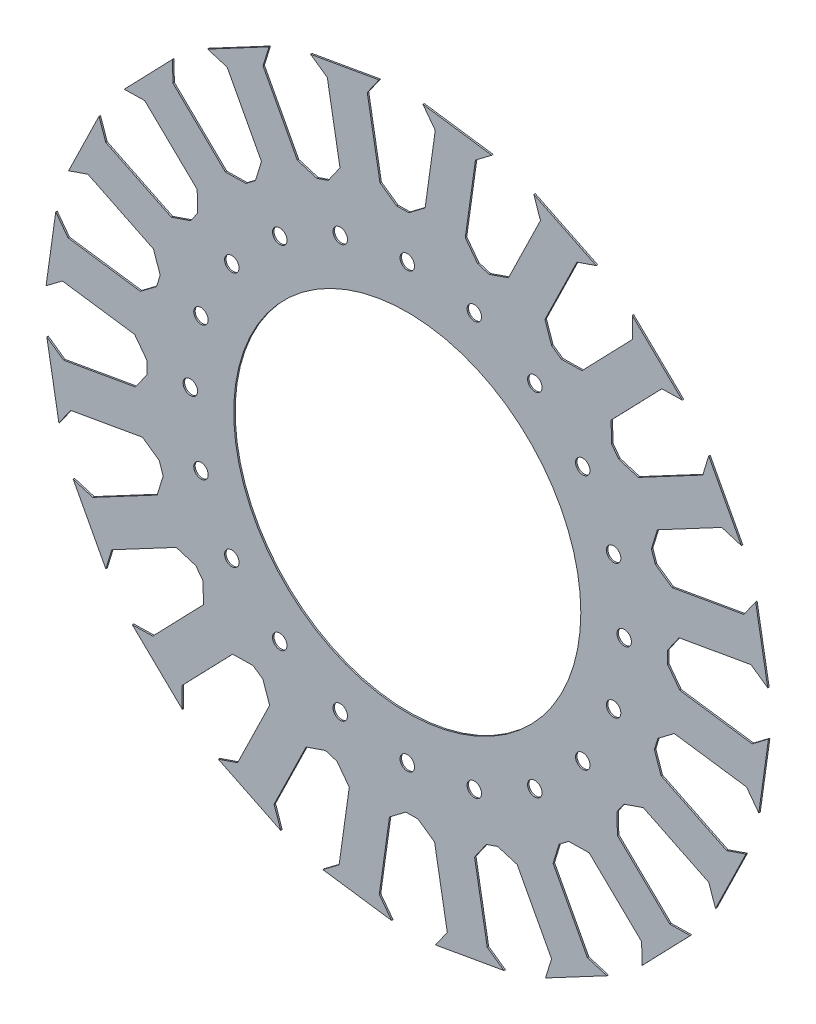
SolidWorks part; units mm, degrees
ref_plane "Ön Düzlem" through (0, 0, 0) normal (0, 0, 1) x (1, 0, 0)
ref_plane "Üst Düzlem" through (0, 0, 0) normal (0, 1, 0) x (1, 0, 0)
ref_plane "Sağ Düzlem" through (0, 0, 0) normal (1, 0, 0) x (0, 0, -1)
sketch "Çizim1" plane through (0, 0, 0) normal (0, 0, 1) x (1, 0, 0)
  line L0 (-3.656, 89.9257) -> (-1.5703, 89.9621)
  line L1 (-27.3209, 85.7529) -> (-29.2933, 85.0738)
  line L2 (-33.438, 120.4446) -> (-9.773, 124.6174)
  line L3 (-9.4482, 93.9815) -> (-13.8288, 118.8251)
  line L4 (-31.2656, 84.3947) -> (-29.2933, 85.0738)
  line L5 (-52.4829, 73.1133) -> (-54.1488, 71.8579)
  line L6 (-69.0208, 104.2167) -> (-47.8036, 115.4981)
  line L7 (-23.2651, 91.5452) -> (-27.6457, 116.3888)
  line L8 (-9.773, 124.6174) -> (-13.8288, 118.8251)
  line L9 (-33.438, 120.4446) -> (-27.6457, 116.3888)
  line L10 (-23.2651, 91.5452) -> (-27.3209, 85.7529)
  line L11 (-9.4482, 93.9815) -> (-3.656, 89.9257)
  line L12 (24.3115, 86.6542) -> (26.3064, 86.0443)
  line L13 (0.5154, 89.9985) -> (-1.5703, 89.9621)
  line L14 (5.418, 124.8825) -> (29.2142, 121.5382)
  line L15 (20.0561, 92.3014) -> (23.567, 117.2827)
  line L16 (6.1626, 94.254) -> (9.6735, 119.2353)
  line L17 (29.2142, 121.5382) -> (23.567, 117.2827)
  line L18 (5.418, 124.8825) -> (9.6735, 119.2353)
  line L19 (6.1626, 94.254) -> (0.5154, 89.9985)
  line L20 (20.0561, 92.3014) -> (24.3115, 86.6542)
  line L21 (49.8993, 74.9004) -> (51.608, 73.7039)
  line L22 (28.3012, 85.4344) -> (26.3064, 86.0443)
  line L23 (43.7437, 117.0961) -> (65.3417, 106.562)
  line L24 (47.5972, 81.5862) -> (58.6559, 104.2599)
  line L25 (34.9871, 87.7365) -> (46.0458, 110.4103)
  line L26 (65.3417, 106.562) -> (58.6559, 104.2599)
  line L27 (43.7437, 117.0961) -> (46.0458, 110.4103)
  line L28 (34.9871, 87.7365) -> (28.3012, 85.4344)
  line L29 (47.5972, 81.5862) -> (49.8993, 74.9004)
  line L30 (70.6025, 55.8147) -> (71.8579, 54.1488)
  line L31 (53.3168, 72.5074) -> (51.608, 73.7039)
  line L32 (77.7874, 97.8475) -> (95.0731, 81.1548)
  line L33 (70.4791, 62.8847) -> (88.0031, 81.0314)
  line L34 (60.3867, 72.6308) -> (77.9108, 90.7775)
  line L35 (95.0731, 81.1548) -> (88.0031, 81.0314)
  line L36 (77.7874, 97.8475) -> (77.9108, 90.7775)
  line L37 (60.3867, 72.6308) -> (53.3168, 72.5074)
  line L38 (70.4791, 62.8847) -> (70.6025, 55.8147)
  line L39 (84.3947, 31.2656) -> (85.0738, 29.2933)
  line L40 (73.1133, 52.4829) -> (71.8579, 54.1488)
  line L41 (104.2167, 69.0208) -> (115.4981, 47.8036)
  line L42 (86.4621, 38.0277) -> (108.736, 49.871)
  line L43 (79.8754, 50.4155) -> (102.1493, 62.2588)
  line L44 (115.4981, 47.8036) -> (108.736, 49.871)
  line L45 (104.2167, 69.0208) -> (102.1493, 62.2588)
  line L46 (79.8754, 50.4155) -> (73.1133, 52.4829)
  line L47 (86.4621, 38.0277) -> (84.3947, 31.2656)
  line L48 (89.9257, 3.656) -> (89.9621, 1.5703)
  line L49 (85.7529, 27.3209) -> (85.0738, 29.2933)
  line L50 (120.4446, 33.438) -> (124.6174, 9.773)
  line L51 (93.9815, 9.4482) -> (118.8251, 13.8288)
  line L52 (91.5452, 23.2651) -> (116.3888, 27.6457)
  line L53 (124.6174, 9.773) -> (118.8251, 13.8288)
  line L54 (120.4446, 33.438) -> (116.3888, 27.6457)
  line L55 (91.5452, 23.2651) -> (85.7529, 27.3209)
  line L56 (93.9815, 9.4482) -> (89.9257, 3.656)
  line L57 (86.6542, -24.3115) -> (86.0443, -26.3064)
  line L58 (89.9985, -0.5154) -> (89.9621, 1.5703)
  line L59 (124.8825, -5.418) -> (121.5382, -29.2142)
  line L60 (92.3014, -20.0561) -> (117.2827, -23.567)
  line L61 (94.254, -6.1626) -> (119.2353, -9.6735)
  line L62 (121.5382, -29.2142) -> (117.2827, -23.567)
  line L63 (124.8825, -5.418) -> (119.2353, -9.6735)
  line L64 (94.254, -6.1626) -> (89.9985, -0.5154)
  line L65 (92.3014, -20.0561) -> (86.6542, -24.3115)
  line L66 (74.9004, -49.8993) -> (73.7039, -51.608)
  line L67 (85.4344, -28.3012) -> (86.0443, -26.3064)
  line L68 (117.0961, -43.7437) -> (106.562, -65.3417)
  line L69 (81.5862, -47.5972) -> (104.2599, -58.6559)
  line L70 (87.7365, -34.9871) -> (110.4103, -46.0458)
  line L71 (106.562, -65.3417) -> (104.2599, -58.6559)
  line L72 (117.0961, -43.7437) -> (110.4103, -46.0458)
  line L73 (87.7365, -34.9871) -> (85.4344, -28.3012)
  line L74 (81.5862, -47.5972) -> (74.9004, -49.8993)
  line L75 (55.8147, -70.6025) -> (54.1488, -71.8579)
  line L76 (72.5074, -53.3168) -> (73.7039, -51.608)
  line L77 (97.8475, -77.7874) -> (81.1548, -95.0731)
  line L78 (62.8847, -70.4791) -> (81.0314, -88.0031)
  line L79 (72.6308, -60.3867) -> (90.7775, -77.9108)
  line L80 (-38.0277, 86.4621) -> (-49.871, 108.736)
  line L81 (81.1548, -95.0731) -> (81.0314, -88.0031)
  line L82 (-50.4155, 79.8754) -> (-62.2588, 102.1493)
  line L83 (97.8475, -77.7874) -> (90.7775, -77.9108)
  line L84 (-47.8036, 115.4981) -> (-49.871, 108.736)
  line L85 (-69.0208, 104.2167) -> (-62.2588, 102.1493)
  line L86 (-50.4155, 79.8754) -> (-52.4829, 73.1133)
  line L87 (-38.0277, 86.4621) -> (-31.2656, 84.3947)
  line L88 (72.6308, -60.3867) -> (72.5074, -53.3168)
  line L90 (-52.4829, 73.1133) -> (-69.0208, 104.2167) construction
  line L92 (-31.2656, 84.3947) -> (-47.8036, 115.4981) construction
  line L93 (-62.2588, 102.1493) -> (-49.871, 108.736) construction
  line L94 (-38.0277, 86.4621) -> (-50.4155, 79.8754) construction
  line L96 (-31.2656, 84.3947) -> (-52.4829, 73.1133) construction
  line L105 (62.8847, -70.4791) -> (55.8147, -70.6025)
  line L106 (31.2656, -84.3947) -> (29.2933, -85.0738)
  line L107 (52.4829, -73.1133) -> (54.1488, -71.8579)
  line L108 (69.0208, -104.2167) -> (47.8036, -115.4981)
  line L109 (38.0277, -86.4621) -> (49.871, -108.736)
  line L110 (50.4155, -79.8754) -> (62.2588, -102.1493)
  line L111 (47.8036, -115.4981) -> (49.871, -108.736)
  line L112 (69.0208, -104.2167) -> (62.2588, -102.1493)
  line L113 (50.4155, -79.8754) -> (52.4829, -73.1133)
  line L114 (38.0277, -86.4621) -> (31.2656, -84.3947)
  line L115 (3.656, -89.9257) -> (1.5703, -89.9621)
  line L116 (27.3209, -85.7529) -> (29.2933, -85.0738)
  line L117 (33.438, -120.4446) -> (9.773, -124.6174)
  line L118 (9.4482, -93.9815) -> (13.8288, -118.8251)
  line L119 (23.2651, -91.5452) -> (27.6457, -116.3888)
  line L120 (9.773, -124.6174) -> (13.8288, -118.8251)
  line L121 (33.438, -120.4446) -> (27.6457, -116.3888)
  line L122 (23.2651, -91.5452) -> (27.3209, -85.7529)
  line L123 (9.4482, -93.9815) -> (3.656, -89.9257)
  line L124 (-24.3115, -86.6542) -> (-26.3064, -86.0443)
  line L125 (-0.5154, -89.9985) -> (1.5703, -89.9621)
  line L126 (-5.418, -124.8825) -> (-29.2142, -121.5382)
  line L127 (-20.0561, -92.3014) -> (-23.567, -117.2827)
  line L128 (-6.1626, -94.254) -> (-9.6735, -119.2353)
  line L129 (-29.2142, -121.5382) -> (-23.567, -117.2827)
  line L130 (-5.418, -124.8825) -> (-9.6735, -119.2353)
  line L131 (-6.1626, -94.254) -> (-0.5154, -89.9985)
  line L132 (-20.0561, -92.3014) -> (-24.3115, -86.6542)
  line L133 (-49.8993, -74.9004) -> (-51.608, -73.7039)
  line L134 (-28.3012, -85.4344) -> (-26.3064, -86.0443)
  line L135 (-43.7437, -117.0961) -> (-65.3417, -106.562)
  line L136 (-47.5972, -81.5862) -> (-58.6559, -104.2599)
  line L137 (-34.9871, -87.7365) -> (-46.0458, -110.4103)
  line L138 (-65.3417, -106.562) -> (-58.6559, -104.2599)
  line L139 (-43.7437, -117.0961) -> (-46.0458, -110.4103)
  line L140 (-34.9871, -87.7365) -> (-28.3012, -85.4344)
  line L141 (-47.5972, -81.5862) -> (-49.8993, -74.9004)
  line L142 (-70.6025, -55.8147) -> (-71.8579, -54.1488)
  line L143 (-53.3168, -72.5074) -> (-51.608, -73.7039)
  line L144 (-77.7874, -97.8475) -> (-95.0731, -81.1548)
  line L145 (-70.4791, -62.8847) -> (-88.0031, -81.0314)
  line L146 (-60.3867, -72.6308) -> (-77.9108, -90.7775)
  line L147 (-95.0731, -81.1548) -> (-88.0031, -81.0314)
  line L148 (-77.7874, -97.8475) -> (-77.9108, -90.7775)
  line L149 (-60.3867, -72.6308) -> (-53.3168, -72.5074)
  line L150 (-70.4791, -62.8847) -> (-70.6025, -55.8147)
  line L151 (-84.3947, -31.2656) -> (-85.0738, -29.2933)
  line L152 (-73.1133, -52.4829) -> (-71.8579, -54.1488)
  line L153 (-104.2167, -69.0208) -> (-115.4981, -47.8036)
  line L154 (-86.4621, -38.0277) -> (-108.736, -49.871)
  line L155 (-79.8754, -50.4155) -> (-102.1493, -62.2588)
  line L156 (-115.4981, -47.8036) -> (-108.736, -49.871)
  line L157 (-104.2167, -69.0208) -> (-102.1493, -62.2588)
  line L158 (-79.8754, -50.4155) -> (-73.1133, -52.4829)
  line L159 (-86.4621, -38.0277) -> (-84.3947, -31.2656)
  line L160 (-89.9257, -3.656) -> (-89.9621, -1.5703)
  line L161 (-85.7529, -27.3209) -> (-85.0738, -29.2933)
  line L162 (-120.4446, -33.438) -> (-124.6174, -9.773)
  line L163 (-93.9815, -9.4482) -> (-118.8251, -13.8288)
  line L164 (-91.5452, -23.2651) -> (-116.3888, -27.6457)
  line L165 (-124.6174, -9.773) -> (-118.8251, -13.8288)
  line L166 (-120.4446, -33.438) -> (-116.3888, -27.6457)
  line L167 (-91.5452, -23.2651) -> (-85.7529, -27.3209)
  line L168 (-93.9815, -9.4482) -> (-89.9257, -3.656)
  line L169 (-86.6542, 24.3115) -> (-86.0443, 26.3064)
  line L170 (-89.9985, 0.5154) -> (-89.9621, -1.5703)
  line L171 (-124.8825, 5.418) -> (-121.5382, 29.2142)
  line L172 (-92.3014, 20.0561) -> (-117.2827, 23.567)
  line L173 (-94.254, 6.1626) -> (-119.2353, 9.6735)
  line L174 (-121.5382, 29.2142) -> (-117.2827, 23.567)
  line L175 (-124.8825, 5.418) -> (-119.2353, 9.6735)
  line L176 (-94.254, 6.1626) -> (-89.9985, 0.5154)
  line L177 (-92.3014, 20.0561) -> (-86.6542, 24.3115)
  line L178 (-74.9004, 49.8993) -> (-73.7039, 51.608)
  line L179 (-85.4344, 28.3012) -> (-86.0443, 26.3064)
  line L180 (-117.0961, 43.7437) -> (-106.562, 65.3417)
  line L181 (-81.5862, 47.5972) -> (-104.2599, 58.6559)
  line L182 (-87.7365, 34.9871) -> (-110.4103, 46.0458)
  line L183 (-106.562, 65.3417) -> (-104.2599, 58.6559)
  line L184 (-117.0961, 43.7437) -> (-110.4103, 46.0458)
  line L185 (-87.7365, 34.9871) -> (-85.4344, 28.3012)
  line L186 (-81.5862, 47.5972) -> (-74.9004, 49.8993)
  line L187 (-55.8147, 70.6025) -> (-54.1488, 71.8579)
  line L188 (-72.5074, 53.3168) -> (-73.7039, 51.608)
  line L189 (-97.8475, 77.7874) -> (-81.1548, 95.0731)
  line L190 (-62.8847, 70.4791) -> (-81.0314, 88.0031)
  line L191 (-72.6308, 60.3867) -> (-90.7775, 77.9108)
  line L192 (-81.1548, 95.0731) -> (-81.0314, 88.0031)
  line L193 (-97.8475, 77.7874) -> (-90.7775, 77.9108)
  line L194 (-72.6308, 60.3867) -> (-72.5074, 53.3168)
  line L195 (-62.8847, 70.4791) -> (-55.8147, 70.6025)
  point P82 (0, 0)
  point P226 (0, 0)
  dimension "D1" = 20
  dimension "D2" = 5
extrude "Yükseklik-Ekstrüzyon1" add sketch "Çizim1" along normal blind 1
sketch "Çizim2" plane through (0, 0, 1) normal (0, 0, 1) x (1, 0, 0)
  circle A0 centre (0, 0) radius 60
extrude "Kes-Ekstrüzyon1" cut sketch "Çizim2" against normal blind 1
sketch "Çizim3" plane through (0, 0, 1) normal (0, 0, 1) x (1, 0, 0)
  circle A0 centre (37.5, 64.9519) radius 2.5
  circle A1 centre (0, 75) radius 2.5
  circle A2 centre (64.9519, 37.5) radius 2.5
  circle A3 centre (75, 0) radius 2.5
  circle A4 centre (64.9519, -37.5) radius 2.5
  circle A5 centre (37.5, -64.9519) radius 2.5
  circle A6 centre (0, -75) radius 2.5
  circle A7 centre (-37.5, -64.9519) radius 2.5
  circle A8 centre (-64.9519, -37.5) radius 2.5
  circle A9 centre (-75, 0) radius 2.5
  circle A10 centre (-64.9519, 37.5) radius 2.5
  circle A11 centre (-37.5, 64.9519) radius 2.5
  point P28 (0, 0)
  dimension "D1" = 12
extrude "Kes-Ekstrüzyon2" cut sketch "Çizim3" against normal blind 1
sketch "Çizim5" plane through (0, 0, 1) normal (0, 0, 1) x (1, 0, 0)
  circle A0 centre (0, 0) radius 60
  circle A1 centre (0, 0) radius 82.2969
extrude "Yükseklik-Ekstrüzyon4" add sketch "Çizim5" against normal blind 1
sketch "Çizim6" plane through (0, 0, 1) normal (0, 0, 1) x (1, 0, 0)
  line L0 (0, 0) -> (0, 75) construction
  line L1 (0, 0) -> (23.1763, 71.3292) construction
  circle A0 centre (23.1763, 71.3292) radius 2.5
  circle A1 centre (0, 75) radius 2.5
  circle A2 centre (44.0839, 60.6763) radius 2.5
  circle A3 centre (60.6763, 44.0839) radius 2.5
  circle A4 centre (71.3292, 23.1763) radius 2.5
  circle A5 centre (75, 0) radius 2.5
  circle A6 centre (71.3292, -23.1763) radius 2.5
  circle A7 centre (60.6763, -44.0839) radius 2.5
  circle A8 centre (44.0839, -60.6763) radius 2.5
  circle A9 centre (23.1763, -71.3292) radius 2.5
  circle A10 centre (0, -75) radius 2.5
  circle A11 centre (-23.1763, -71.3292) radius 2.5
  circle A12 centre (-44.0839, -60.6763) radius 2.5
  circle A13 centre (-60.6763, -44.0839) radius 2.5
  circle A14 centre (-71.3292, -23.1763) radius 2.5
  circle A15 centre (-75, 0) radius 2.5
  circle A16 centre (-71.3292, 23.1763) radius 2.5
  circle A17 centre (-60.6763, 44.0839) radius 2.5
  circle A18 centre (-44.0839, 60.6763) radius 2.5
  circle A19 centre (-23.1763, 71.3292) radius 2.5
  dimension "D1" = 20
  dimension "D2" = 18
extrude "Kes-Ekstrüzyon3" cut sketch "Çizim6" against normal blind 1
sketch "Çizim7" plane through (0, 0, 1) normal (0, 0, 1) x (1, 0, 0)
  circle A0 centre (0, 0) radius 160.4632
extrude "Kes-Ekstrüzyon4" cut sketch "Çizim7" against normal blind 0.5
